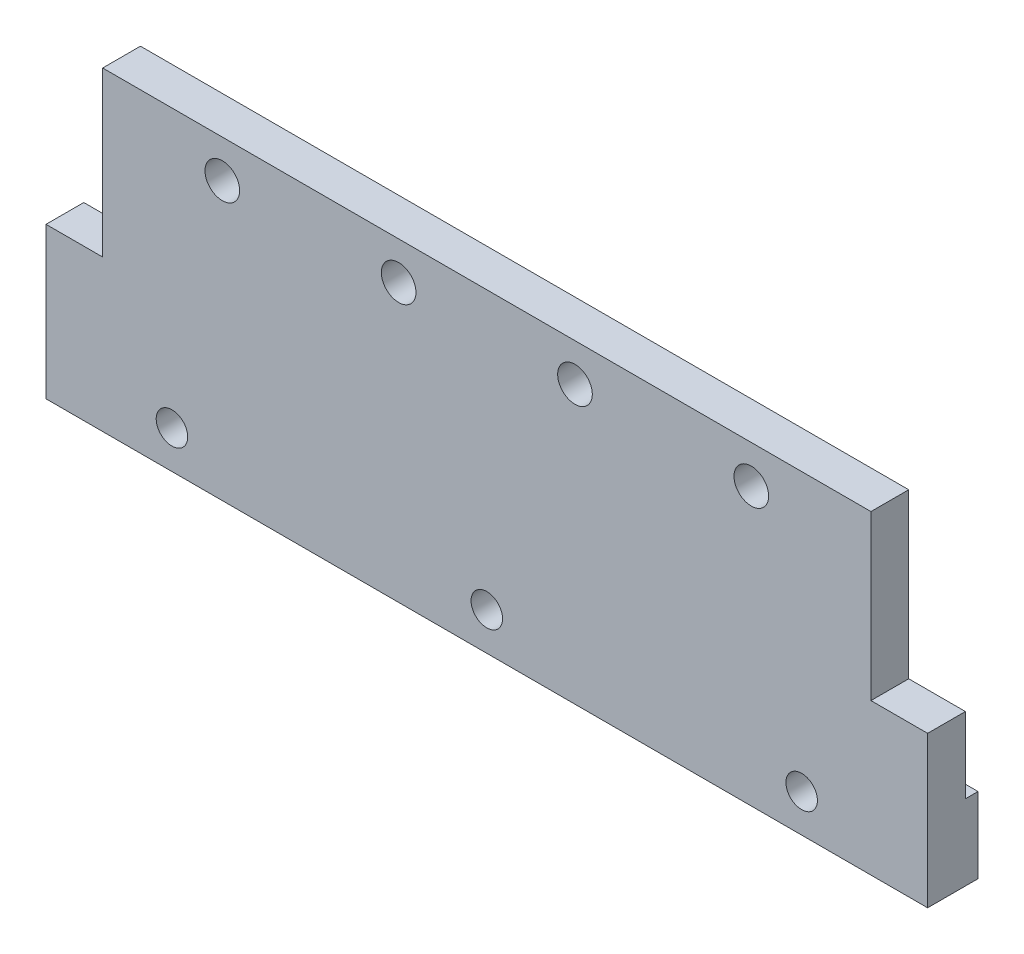
SolidWorks part; units mm, degrees
material " 09Г2С ГОСТ 4543-71"
ref_plane "Спереди" through (0, 0, 0) normal (0, 0, 1) x (1, 0, 0)
ref_plane "Сверху" through (0, 0, 0) normal (0, 1, 0) x (1, 0, 0)
ref_plane "Слева" through (0, 0, 0) normal (1, 0, 0) x (0, 0, -1)
sketch "Эскиз1" plane through (0, 0, 0) normal (0, 0, 1) x (1, 0, 0)
  line L0 (-70, 19) -> (70, 19) construction
  line L1 (-70, -25) -> (70, -25)
  line L2 (-70, -25) -> (-70, 25)
  line L3 (-70, 25) -> (70, 25)
  line L4 (70, -25) -> (70, 25)
  line L5 (-70, -25) -> (70, 25) construction
  line L6 (-70, 25) -> (70, -25) construction
  circle A0 centre (-42, 19) radius 2.75 construction
  circle A1 centre (-14, 19) radius 2.75 construction
  circle A2 centre (14, 19) radius 2.75 construction
  circle A3 centre (42, 19) radius 2.75 construction
  point P0 (0, 0)
  dimension "D4" = 28
  dimension "D5" = 28
  dimension "D6" = 28
  dimension "D7" = 28
  dimension "D8" = 5.5
  dimension "D10" = 3.25
  dimension "D1" = 50
  dimension "D2" = 140
  dimension "D3" = 28
  dimension "D9" = 6
extrude "Вытянуть1" add sketch "Эскиз1" along normal blind 6
sketch "Эскиз6" plane through (0, 0, 0) normal (0, 0, -1) x (-1, 0, 0)
  circle A0 centre (42, 19) radius 2.75 construction
  circle A1 centre (14, 19) radius 2.75 construction
  circle A2 centre (-14, 19) radius 2.75 construction
  circle A3 centre (-42, 19) radius 2.75 construction
  circle A4 centre (42, 19) radius 2.75
  circle A5 centre (14, 19) radius 2.75
  circle A6 centre (-14, 19) radius 2.75
  circle A7 centre (-42, 19) radius 2.75
extrude "Вытянуть4" cut sketch "Эскиз6" against normal through all
sketch "Эскиз7" [suppressed] plane through (0, 0, 0) normal (0, 0, -1) x (-1, 0, 0)
  line L0 (70, 19) -> (-70, 19) construction
  circle A0 centre (-42, 19) radius 3.25
  circle A1 centre (0, 19) radius 3.25
  circle A2 centre (42, 19) radius 3.25
  dimension "D1" = 6.5
extrude "Вытянуть5" [suppressed] cut sketch "Эскиз7" against normal through all
sketch "Эскиз5" plane through (0, 0, 0) normal (0, 0, -1) x (-1, 0, 0)
  line L0 (-70, -25) -> (-70, 25) construction
  line L1 (70, -25) -> (-70, -25)
  line L2 (70, -25) -> (70, -13)
  line L3 (70, -13) -> (-70, -13)
  line L4 (-70, -25) -> (-70, -13)
  dimension "D1" = 12
extrude "Вытянуть3" add sketch "Эскиз5" along normal blind 2
hole_wizard "Отверстие обработанное метчиком M6x1.01" positions "Эскиз3" profile "Эскиз2" tap size "M6x1.0" standard "ГОСТ" end condition through all
sketch "Эскиз3" plane through (0, 0, 6) normal (0, 0, 1) x (1, 0, 0)
  line L0 (-70, -19) -> (70, -19) construction
  line L1 (-70, 25) -> (-70, -25) construction
  line L2 (70, -25) -> (70, 25) construction
  line L4 (-70, -25) -> (70, -25) construction
  point P0 (0, -19)
  point P12 (-50, -19)
  point P14 (50, -19)
  dimension "D1" = 6
  dimension "D2" = 50
  dimension "D3" = 50
  dimension "D4" = 20
  dimension "D5" = 20
sketch "Эскиз2" plane through (0, -19, 6) normal (1, 0, 0) x (0, -1, 0)
  line L0 (0, 0) -> (0, 8)
  line L1 (0, 8) -> (3.25, 8)
  line L2 (2.5, 7.25) -> (2.5, 0)
  line L5 (2.5, 0) -> (0, 0)
  line L7 (3.25, 8) -> (2.5, 7.25)
  line L8 (-3.25, 8) -> (-2.5, 7.25) construction
  line L11 (0, -6.35) -> (0, 107.95) construction
  dimension "Диаметр проходного сверла" = 5
  dimension "Глубина проходного сверла" = 8
  dimension "Диаметр задней зенковки" = 6.5
  dimension "Угол задней зенковки" = 90
cosmetic thread "Отверстие резьбы1" parameters "D2"=6
cosmetic thread "Отверстие резьбы2" parameters "D2"=6
cosmetic thread "Отверстие резьбы3" parameters "D2"=6
sketch "Эскиз4" plane through (0, 0, 6) normal (0, 0, 1) x (1, 0, 0)
  line L1 (-70, 25) -> (-61, 25)
  line L2 (-70, 25) -> (-70, -1)
  line L3 (-70, -1) -> (-61, -1)
  line L4 (-61, 25) -> (-61, -1)
  line L5 (70, 25) -> (61, 25)
  line L6 (70, 25) -> (70, -1)
  line L7 (70, -1) -> (61, -1)
  line L8 (61, 25) -> (61, -1)
  dimension "D1" = 26
  dimension "D2" = 9
extrude "Вытянуть2" cut sketch "Эскиз4" against normal through all
